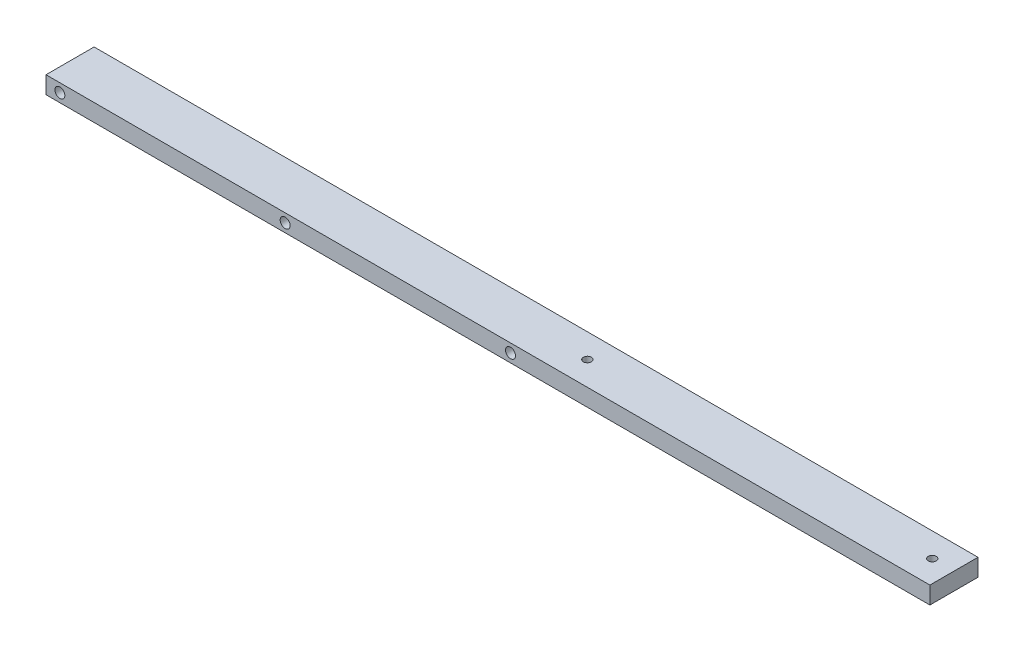
SolidWorks part; units mm, degrees
ref_plane "Front Plane" through (0, 0, 0) normal (0, 0, 1) x (1, 0, 0)
ref_plane "Top Plane" through (0, 0, 0) normal (0, 1, 0) x (1, 0, 0)
ref_plane "Right Plane" through (0, 0, 0) normal (1, 0, 0) x (0, 0, -1)
sketch "Sketch1" plane through (0, 0, 0) normal (1, 0, 0) x (0, 0, -1)
  line L1 (0, 0) -> (17.6276, 0)
  line L2 (0, 0) -> (0, 6.35)
  line L3 (0, 6.35) -> (17.6276, 6.35)
  line L4 (17.6276, 0) -> (17.6276, 6.35)
  dimension "D1" = 17.6276
  dimension "D2" = 6.35
extrude "Boss-Extrude1" add sketch "Sketch1" along normal blind 323.85
hole_wizard "#6 Clearance Hole1" positions "Sketch3" profile "Sketch2" hole size "#6" standard "ANSI Inch" end condition through all
sketch "Sketch3" plane through (0, 0, 0) normal (0, 0, 1) x (1, 0, 0)
  line L0 (0, 6.35) -> (0, 0) construction
  line L1 (323.85, 3.175) -> (0, 3.175) construction
  line L2 (323.85, 6.35) -> (323.85, 0) construction
  point P0 (5.08, 3.175)
  point P2 (87.63, 3.175)
  point P4 (170.18, 3.175)
  point P7 (0, 3.175)
  dimension "D1" = 5.08
  dimension "D2" = 82.55
  dimension "D3" = 82.55
sketch "Sketch2" plane through (5.08, 3.175, 0) normal (1, 0, 0) x (0, -1, 0)
  line L0 (0, 0) -> (0, 17.6276)
  line L1 (0, 17.6276) -> (1.8288, 17.6276)
  line L2 (1.8288, 17.6276) -> (1.8288, 0)
  line L5 (1.8288, 0) -> (0, 0)
  line L11 (0, -6.35) -> (0, 107.95) construction
  dimension "Thru Hole Dia." = 3.6576
  dimension "Thru Hole Depth" = 17.6276
hole_wizard "CBORE for #4 Binding Head Machine Screw2" positions "Sketch5" profile "Sketch4" counterbore size "#4" standard "ANSI Inch" end condition through all
sketch "Sketch5" plane through (0, 0, 0) normal (0, -1, 0) x (-1, 0, 0)
  line L2 (-323.85, 17.6276) -> (0, 17.6276) construction
  line L3 (0, 17.6276) -> (0, 0) construction
  point P0 (-315.9125, 8.8138)
  point P8 (-189.5475, 8.8138)
  dimension "D1" = 189.5475
  dimension "D2" = 8.8138
  dimension "D3" = 126.365
  dimension "D4" = 8.8138
sketch "Sketch4" plane through (315.9125, 0, -8.8138) normal (1, 0, 0) x (0, 0, -1)
  line L0 (0, 0) -> (0, 6.35)
  line L1 (0, 6.35) -> (1.4732, 6.35)
  line L3 (1.4732, 6.35) -> (1.4732, 2.8448)
  line L4 (1.4732, 2.8448) -> (2.4003, 2.8448)
  line L5 (2.4003, 2.8448) -> (2.4003, 0)
  line L7 (2.4003, 0) -> (0, 0)
  line L11 (0, -6.35) -> (0, 107.95) construction
  dimension "Thru Hole Dia." = 2.9464
  dimension "Thru Hole Depth" = 6.35
  dimension "C'Bore Dia." = 4.8006
  dimension "C'Bore Depth" = 2.8448
